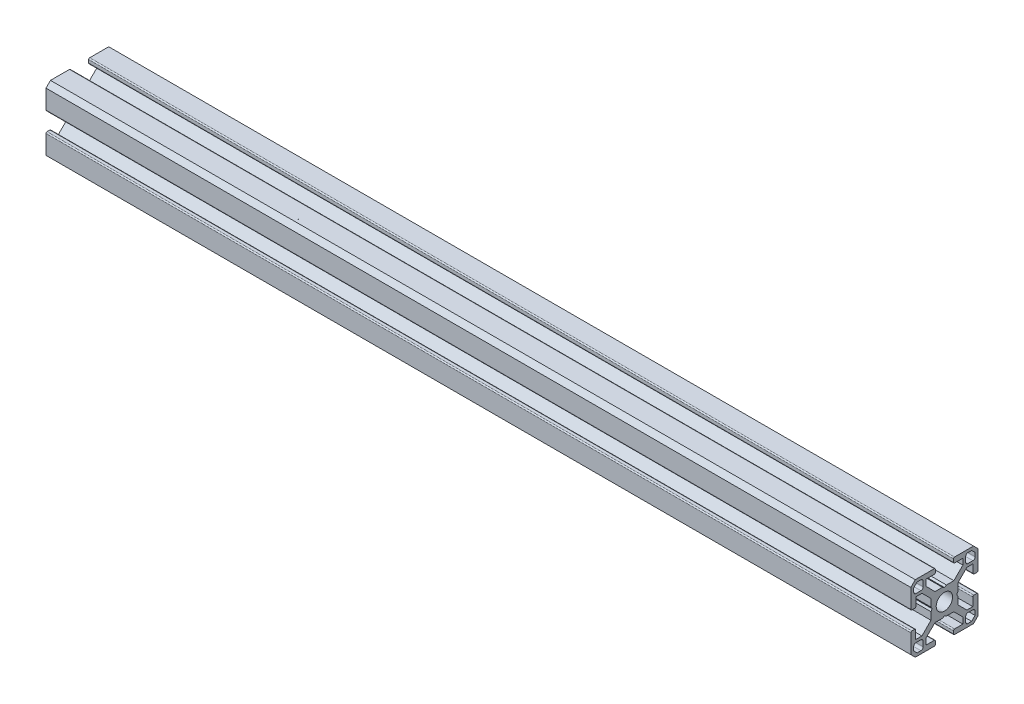
SolidWorks part; units mm, degrees
material "6061 Alloy"
ref_plane "Front Plane" through (0, 0, 0) normal (0, 0, 1) x (1, 0, 0)
ref_plane "Top Plane" through (0, 0, 0) normal (0, 1, 0) x (1, 0, 0)
ref_plane "Right Plane" through (0, 0, 0) normal (1, 0, 0) x (0, 0, -1)
ref_plane "CENTER" through (0, 0, 0) normal (-1, 0, 0) x (0, -1, 0)
sketch "Sketch1" plane through (0, 0, 0) normal (-1, 0, 0) x (0, -1, 0)
  line L0 (4.55, -15) -> (12.9999, -15)
  line L1 (12.9999, -15) -> (15, -12.9999)
  line L2 (15, -12.9999) -> (15, -4.55)
  line L3 (14.5, -4.05) -> (13.3, -4.05)
  line L4 (12.8, -4.55) -> (12.8, -8.25)
  line L5 (12.8, -8.25) -> (10.0489, -8.25)
  line L6 (10.0489, -8.25) -> (6, -4.2011)
  line L7 (6, -4.2011) -> (6, -0.8992)
  line L8 (6, -0.8992) -> (5.485, 0)
  line L9 (5.485, 0) -> (6, 0.8992)
  line L10 (6, 0.8992) -> (6, 4.2322)
  line L11 (6, 4.2322) -> (10.0177, 8.25)
  line L12 (10.0177, 8.25) -> (12.6816, 8.25)
  line L13 (12.6816, 8.25) -> (12.6816, 4.55)
  line L14 (13.1816, 4.05) -> (14.5, 4.05)
  line L15 (15, 4.55) -> (15, 12.9999)
  line L16 (15, 12.9999) -> (12.9999, 15)
  line L17 (12.9999, 15) -> (4.55, 15)
  line L18 (4.05, 14.5) -> (4.05, 13.3)
  line L19 (4.55, 12.8) -> (8.25, 12.8)
  line L20 (8.25, 12.8) -> (8.25, 10.0489)
  line L21 (8.25, 10.0489) -> (4.2011, 6)
  line L22 (4.2011, 6) -> (0.8992, 6)
  line L23 (0.8992, 6) -> (0, 5.485)
  line L24 (0, 5.485) -> (-0.8992, 6)
  line L25 (-0.8992, 6) -> (-4.2322, 6)
  line L26 (-4.2322, 6) -> (-8.25, 10.0177)
  line L27 (-8.25, 10.0177) -> (-8.25, 12.6816)
  line L28 (-8.25, 12.6816) -> (-4.55, 12.6816)
  line L29 (-4.05, 13.1816) -> (-4.05, 14.5)
  line L30 (-4.55, 15) -> (-12.9999, 15)
  line L31 (-12.9999, 15) -> (-15, 12.9999)
  line L32 (-15, 12.9999) -> (-15, 4.55)
  line L33 (-14.5, 4.05) -> (-13.3, 4.05)
  line L34 (-12.8, 4.55) -> (-12.8, 8.25)
  line L35 (-12.8, 8.25) -> (-10.0489, 8.25)
  line L36 (-10.0489, 8.25) -> (-6, 4.2011)
  line L37 (-6, 4.2011) -> (-6, 0.8992)
  line L38 (-6, 0.8992) -> (-5.485, 0)
  line L39 (-5.485, 0) -> (-6, -0.8992)
  line L40 (-6, -0.8992) -> (-6, -4.2322)
  line L41 (-6, -4.2322) -> (-10.0177, -8.25)
  line L42 (-10.0177, -8.25) -> (-12.6816, -8.25)
  line L43 (-12.6816, -8.25) -> (-12.6816, -4.55)
  line L44 (-13.1816, -4.05) -> (-14.5, -4.05)
  line L45 (-15, -4.55) -> (-15, -12.9999)
  line L46 (-15, -12.9999) -> (-12.9999, -15)
  line L47 (-12.9999, -15) -> (-4.55, -15)
  line L48 (-4.05, -14.5) -> (-4.05, -13.3)
  line L49 (-4.55, -12.8) -> (-8.25, -12.8)
  line L50 (-8.25, -12.8) -> (-8.25, -10.0489)
  line L51 (-8.25, -10.0489) -> (-4.2011, -6)
  line L52 (-4.2011, -6) -> (-0.8992, -6)
  line L53 (-0.8992, -6) -> (0, -5.485)
  line L54 (0, -5.485) -> (0.8992, -6)
  line L55 (0.8992, -6) -> (4.2322, -6)
  line L56 (4.2322, -6) -> (8.25, -10.0177)
  line L57 (8.25, -10.0177) -> (8.25, -12.6816)
  line L58 (8.25, -12.6816) -> (4.55, -12.6816)
  line L59 (4.05, -13.1816) -> (4.05, -14.5)
  line L60 (-10.5, 9.5) -> (-12.7, 9.5)
  line L61 (-13.7, 10.5) -> (-13.7, 12.1787)
  line L62 (-13.7, 12.1787) -> (-12.1787, 13.7)
  line L63 (-12.1787, 13.7) -> (-10.5, 13.7)
  line L64 (-9.5, 12.7) -> (-9.5, 10.5)
  line L65 (9.5, 10.5) -> (9.5, 12.7)
  line L66 (10.5, 13.7) -> (12.1787, 13.7)
  line L67 (12.1787, 13.7) -> (13.7, 12.1787)
  line L68 (13.7, 12.1787) -> (13.7, 10.5)
  line L69 (12.7, 9.5) -> (10.5, 9.5)
  line L70 (10.5, -9.5) -> (12.7, -9.5)
  line L71 (13.7, -10.5) -> (13.7, -12.1787)
  line L72 (13.7, -12.1787) -> (12.1787, -13.7)
  line L73 (12.1787, -13.7) -> (10.5, -13.7)
  line L74 (9.5, -12.7) -> (9.5, -10.5)
  line L75 (-9.5, -10.5) -> (-9.5, -12.7)
  line L76 (-10.5, -13.7) -> (-12.1787, -13.7)
  line L77 (-12.1787, -13.7) -> (-13.7, -12.1787)
  line L78 (-13.7, -12.1787) -> (-13.7, -10.5)
  line L79 (-12.7, -9.5) -> (-10.5, -9.5)
  arc A0 (15, -4.55) -> (14.5, -4.05) centre (14.5, -4.55) ccw
  arc A1 (13.3, -4.05) -> (12.8, -4.55) centre (13.3, -4.55) ccw
  arc A2 (12.6816, 4.55) -> (13.1816, 4.05) centre (13.1816, 4.55) ccw
  arc A3 (14.5, 4.05) -> (15, 4.55) centre (14.5, 4.55) ccw
  arc A4 (4.55, 15) -> (4.05, 14.5) centre (4.55, 14.5) ccw
  arc A5 (4.05, 13.3) -> (4.55, 12.8) centre (4.55, 13.3) ccw
  arc A6 (-4.55, 12.6816) -> (-4.05, 13.1816) centre (-4.55, 13.1816) ccw
  arc A7 (-4.05, 14.5) -> (-4.55, 15) centre (-4.55, 14.5) ccw
  arc A8 (-15, 4.55) -> (-14.5, 4.05) centre (-14.5, 4.55) ccw
  arc A9 (-13.3, 4.05) -> (-12.8, 4.55) centre (-13.3, 4.55) ccw
  arc A10 (-12.6816, -4.55) -> (-13.1816, -4.05) centre (-13.1816, -4.55) ccw
  arc A11 (-14.5, -4.05) -> (-15, -4.55) centre (-14.5, -4.55) ccw
  arc A12 (-4.55, -15) -> (-4.05, -14.5) centre (-4.55, -14.5) ccw
  arc A13 (-4.05, -13.3) -> (-4.55, -12.8) centre (-4.55, -13.3) ccw
  arc A14 (4.55, -12.6816) -> (4.05, -13.1816) centre (4.55, -13.1816) ccw
  arc A15 (4.05, -14.5) -> (4.55, -15) centre (4.55, -14.5) ccw
  circle A16 centre (0, 0) radius 3.65
  arc A17 (-12.7, 9.5) -> (-13.7, 10.5) centre (-12.7, 10.5) cw
  arc A18 (-10.5, 13.7) -> (-9.5, 12.7) centre (-10.5, 12.7) cw
  arc A19 (-9.5, 10.5) -> (-10.5, 9.5) centre (-10.5, 10.5) cw
  arc A20 (9.5, 12.7) -> (10.5, 13.7) centre (10.5, 12.7) cw
  arc A21 (13.7, 10.5) -> (12.7, 9.5) centre (12.7, 10.5) cw
  arc A22 (10.5, 9.5) -> (9.5, 10.5) centre (10.5, 10.5) cw
  arc A23 (12.7, -9.5) -> (13.7, -10.5) centre (12.7, -10.5) cw
  arc A24 (10.5, -13.7) -> (9.5, -12.7) centre (10.5, -12.7) cw
  arc A25 (9.5, -10.5) -> (10.5, -9.5) centre (10.5, -10.5) cw
  arc A26 (-9.5, -12.7) -> (-10.5, -13.7) centre (-10.5, -12.7) cw
  arc A27 (-13.7, -10.5) -> (-12.7, -9.5) centre (-12.7, -10.5) cw
  arc A28 (-10.5, -9.5) -> (-9.5, -10.5) centre (-10.5, -10.5) cw
  dimension "D1" = 7.3
extrude "main Extrude" add sketch "Sketch1" against normal mid plane 386.08
equation "\"length\"=386.08"
equation "\"D1@main Extrude\" = \"length\""
